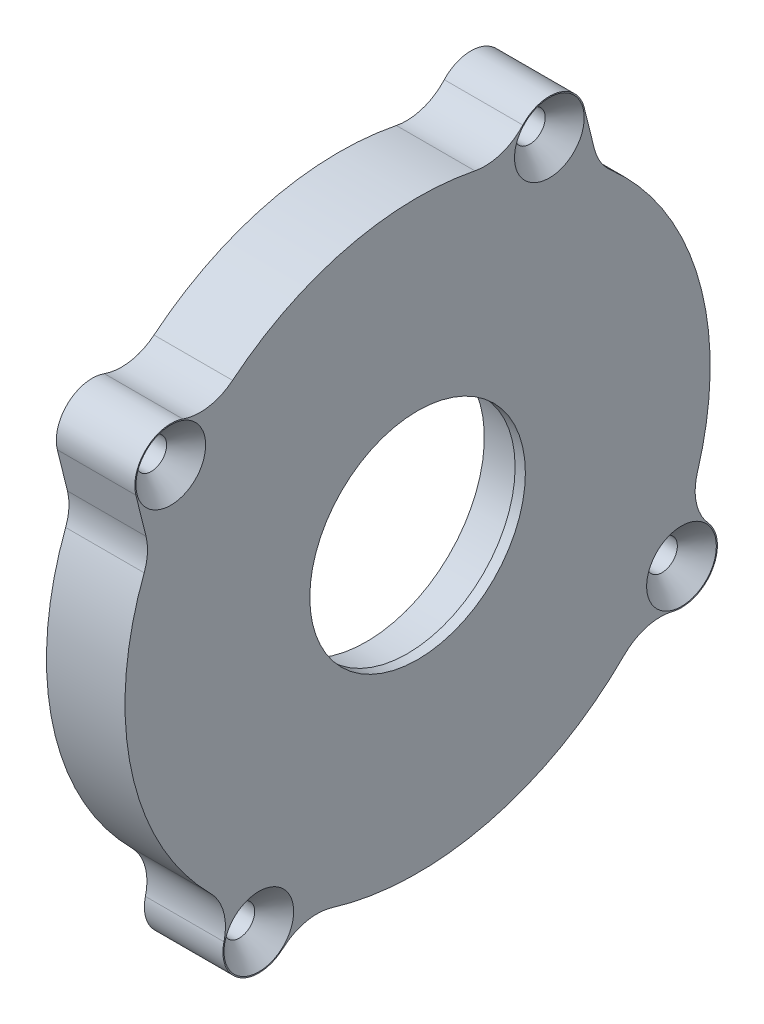
SolidWorks part; units mm, degrees
material "6061 Alloy"
ref_plane "Front" through (0, 0, 0) normal (0, 0, 1) x (1, 0, 0)
ref_plane "Top" through (0, 0, 0) normal (0, 1, 0) x (1, 0, 0)
ref_plane "Right" through (0, 0, 0) normal (1, 0, 0) x (0, 0, -1)
sketch "Sketch1" plane through (0, 0, 0) normal (0, 0, 1) x (1, 0, 0)
  line L0 (0, 0) -> (61.1953, 0) construction
  line L1 (-6.3164, 28.5) -> (1.3336, 28.5)
  line L2 (1.3336, 28.5) -> (1.3336, 10.5)
  line L3 (-0.6664, 11.5) -> (-3.6664, 11.5)
  line L4 (-3.6664, 11.5) -> (-3.6664, 13)
  line L5 (1.3336, 10.5) -> (0.3336, 10.5)
  line L6 (0.3336, 10.5) -> (0.3336, 11.5)
  line L7 (0.3336, 11.5) -> (-0.6664, 11.5)
  line L8 (-0.6664, 11.5) -> (-0.6664, 26.5)
  line L9 (-0.6664, 26.5) -> (-6.8164, 26.5)
  line L10 (-6.8164, 26.5) -> (-6.8164, 27.5)
  line L11 (-6.8164, 27.5) -> (-6.3164, 27.5)
  line L12 (-6.3164, 27.5) -> (-6.3164, 28.5)
  line L13 (-3.6664, 13) -> (-0.6664, 13)
  dimension "D1" = 10.5
  dimension "D2" = 11.5
  dimension "D3" = 26.5
  dimension "D4" = 28.5
  dimension "D5" = 0.5
  dimension "D6" = 1
  dimension "D7" = 2
  dimension "D8" = 1.5
  dimension "D9" = 4
  dimension "D10" = 1
  dimension "D11" = 6.15
revolve "Revolve1" add sketch "Sketch1" angle 360 about L0
sketch "Sketch2" plane through (-6.3164, 0, 0) normal (-1, 0, 0) x (0, 0, 1)
  circle A0 centre (-12.8337, 27.1164) radius 1.495
  circle A1 centre (-12.8337, 27.1164) radius 3.5
  circle A2 centre (24.0425, 17.9432) radius 1.495
  circle A3 centre (24.0425, 17.9432) radius 3.5
  circle A4 centre (15.465, -25.7067) radius 1.495
  circle A5 centre (15.465, -25.7067) radius 3.5
  circle A6 centre (-25.7067, -15.465) radius 1.495
  circle A7 centre (-25.7067, -15.465) radius 3.5
  circle M1 centre (0, 0) radius 28.5
  dimension "D1" = 2.99
  dimension "D2" = 2.99
  dimension "D3" = 2.99
  dimension "D4" = 2.99
extrude "Boss-Extrude1" add sketch "Sketch2" against normal up to surface (7.65 mm away) contours A1 A0 M1 | A3 A2 M1 | A7 A6 M1 | A5 A4 M1
fillet "Fillet1" radius 5 6 edges at (-2.4914, 26.9265, -9.3388) (-2.4914, 19.4129, 20.866) (-2.4914, -11.9686, -25.8651) (-2.4914, -17.2431, -22.692) (-2.4914, -25.8651, 11.9686) (-2.4914, -22.692, 17.2431)
chamfer "Chamfer1" distance 1.9 angle 45 4 edges at (1.3336, -25.7067, 13.97) (1.3336, -15.465, -27.2017) (1.3336, 27.1164, -14.3287) (1.3336, 17.9432, 22.5475)
sketch "Sketch4" plane through (-6.3164, 0, 0) normal (-1, 0, 0) x (0, 0, 1)
  line L0 (-16.2302, 27.9613) -> (27.439, 17.0983)
  line L1 (-16.2302, 27.9613) -> (-19.2215, 15.9361)
  line L2 (27.439, 17.0983) -> (24.4477, 5.0731)
  line L3 (-19.2215, 15.9361) -> (24.4477, 5.0731)
  arc A0 (-10.2504, 29.4779) -> (-14.9025, 24.2933) centre (-12.8337, 27.1164) ccw construction
  arc A1 (24.5476, 14.4798) -> (22.8667, 21.2398) centre (24.0425, 17.9432) ccw construction
  circle A3 centre (-12.8337, 27.1164) radius 1.495 construction
  circle A4 centre (24.0425, 17.9432) radius 1.495 construction
  point P10 (-12.8337, 27.1164)
  point P14 (24.0425, 17.9432)
  arc M4 (-14.9025, 24.2933) -> (-27.2552, -8.3308) centre (0, 0) ccw
  arc M12 (20.1756, -20.1295) -> (24.5476, 14.4798) centre (0, 0) ccw
  arc M13 (24.5476, 14.4798) -> (22.8667, 21.2398) centre (24.0425, 17.9432) ccw
  arc M17 (-10.2504, 29.4779) -> (-14.9025, 24.2933) centre (-12.8337, 27.1164) ccw
extrude "Boss-Extrude2" add sketch "Sketch4" against normal up to surface (7.65 mm away) contours L1 M17 M4 | L2 M13 M12
fillet "Fillet2" radius 5 2 edges at (-2.4914, 11.544, 26.0573) (-2.4914, 22.407, -17.6118)
